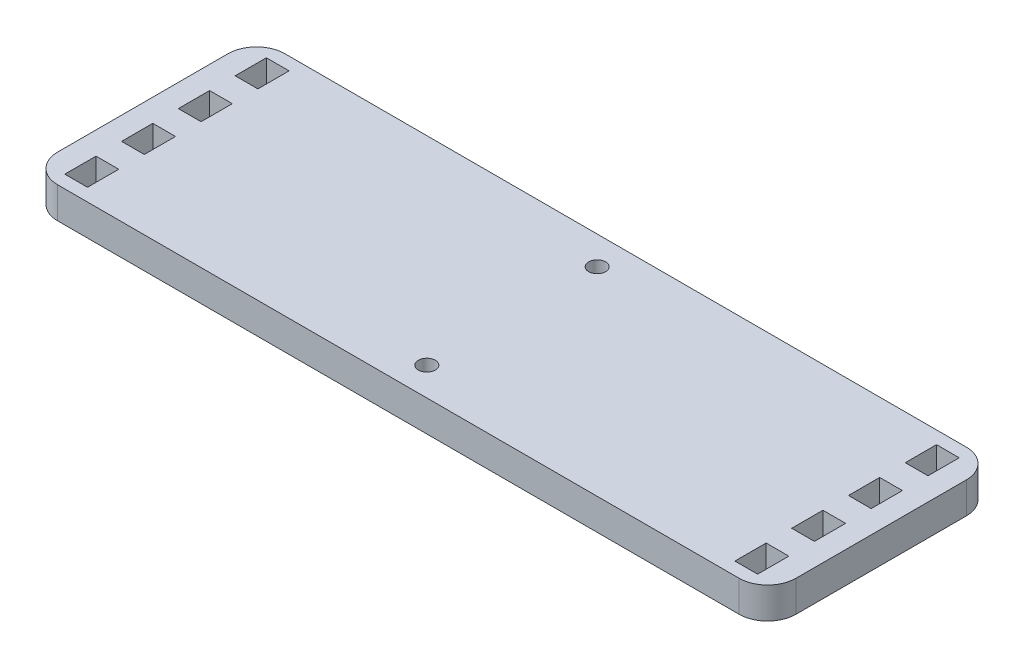
SolidWorks part; units mm, degrees
ref_plane "Front Plane" through (0, 0, 0) normal (0, 0, 1) x (1, 0, 0)
ref_plane "Top Plane" through (0, 0, 0) normal (0, 1, 0) x (1, 0, 0)
ref_plane "Right Plane" through (0, 0, 0) normal (1, 0, 0) x (0, 0, -1)
sketch "Sketch1" plane through (0, 0, 0) normal (0, 1, 0) x (1, 0, 0)
  line L1 (65, -20) -> (-65, -20)
  line L2 (65, -20) -> (65, 20)
  line L3 (65, 20) -> (-65, 20)
  line L4 (-65, -20) -> (-65, 20)
  line L5 (65, -20) -> (-65, 20) construction
  line L6 (65, 20) -> (-65, -20) construction
  circle A0 centre (0, 15) radius 1.5
  circle A1 centre (0, -15) radius 1.5
  point P0 (0, 0)
  dimension "D3" = 15
  dimension "D4" = 3
  dimension "D1" = 130
  dimension "D2" = 40
  dimension "15mm" = 15
extrude "Boss-Extrude1" add sketch "Sketch1" along normal blind 5.5
sketch "Sketch2" plane through (0, 5.5, 0) normal (0, 1, 0) x (1, 0, 0)
  line L1 (65, 20) -> (-65, 20) construction
  line L2 (-65, -20) -> (65, -20) construction
  line L3 (0, 20) -> (0, -20) construction
  line L4 (-59, 20) -> (-59, -20) construction
  line L5 (-65, 20) -> (-65, -20) construction
  line L6 (-57, 7.75) -> (-57, 2.25)
  line L7 (-61, 17.75) -> (-57, 17.75)
  line L8 (-61, 17.75) -> (-61, 12.25)
  line L9 (-61, 12.25) -> (-57, 12.25)
  line L10 (-57, 17.75) -> (-57, 12.25)
  line L11 (-61, 17.75) -> (-57, 12.25) construction
  line L12 (-61, 12.25) -> (-57, 17.75) construction
  line L13 (-61, 7.75) -> (-57, 7.75)
  line L14 (-61, 7.75) -> (-61, 2.25)
  line L15 (-61, 2.25) -> (-57, 2.25)
  line L16 (-57, -2.25) -> (-57, -7.75)
  line L17 (-61, -2.25) -> (-57, -2.25)
  line L18 (-61, -2.25) -> (-61, -7.75)
  line L19 (-61, -7.75) -> (-57, -7.75)
  line L20 (-57, -12.25) -> (-57, -17.75)
  line L21 (-61, -12.25) -> (-57, -12.25)
  line L22 (-61, -12.25) -> (-61, -17.75)
  line L23 (-61, -17.75) -> (-57, -17.75)
  line L24 (61, -17.75) -> (57, -17.75)
  line L25 (57, -12.25) -> (57, -17.75)
  line L26 (61, -12.25) -> (61, -17.75)
  line L27 (61, -12.25) -> (57, -12.25)
  line L28 (61, 17.75) -> (57, 17.75)
  line L29 (57, 17.75) -> (57, 12.25)
  line L30 (61, 12.25) -> (57, 12.25)
  line L31 (61, 17.75) -> (61, 12.25)
  line L32 (61, -7.75) -> (57, -7.75)
  line L33 (57, -2.25) -> (57, -7.75)
  line L34 (61, -2.25) -> (61, -7.75)
  line L35 (61, -2.25) -> (57, -2.25)
  line L36 (61, 2.25) -> (57, 2.25)
  line L37 (57, 7.75) -> (57, 2.25)
  line L38 (61, 7.75) -> (61, 2.25)
  line L39 (61, 7.75) -> (57, 7.75)
  point P13 (-59, 15)
  dimension "D1" = 6
  dimension "D2" = 5
  dimension "D3" = 5.5
  dimension "D4" = 4
  dimension "D5" = 4
extrude "Cut-Extrude1" cut sketch "Sketch2" against normal through all
fillet "Fillet1" radius 5 4 edges at (65, 2.75, -20) (-65, 2.75, -20) (-65, 2.75, 20) (65, 2.75, 20)
